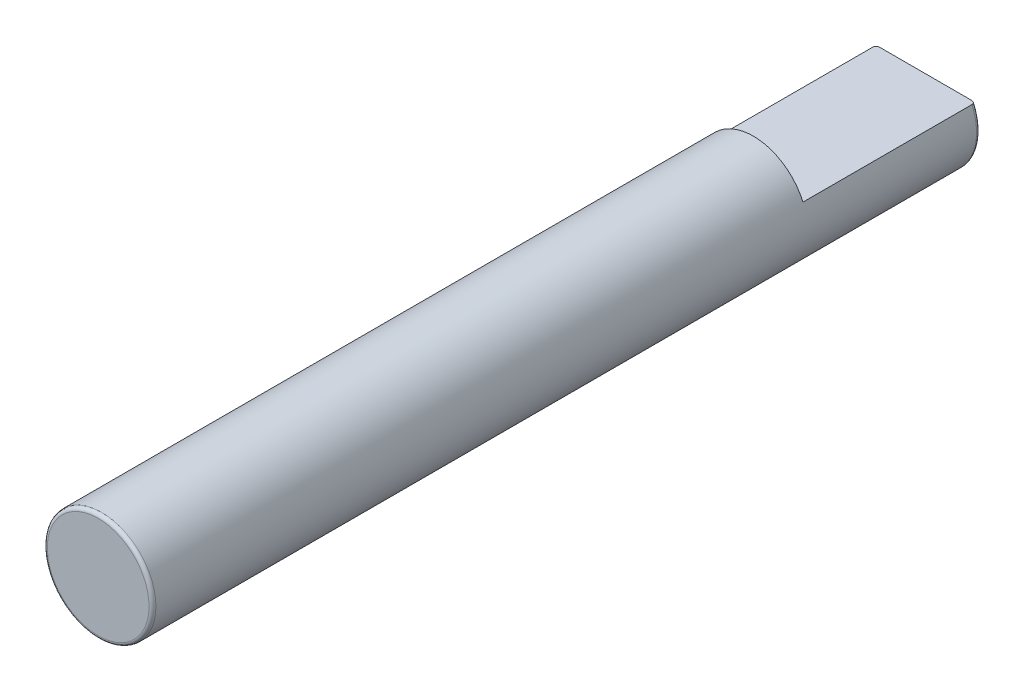
SolidWorks part; units mm, degrees
material "AISI Type 316L stainless steel"
ref_plane "Front Plane" through (0, 0, 0) normal (0, 0, 1) x (1, 0, 0)
ref_plane "Top Plane" through (0, 0, 0) normal (0, 1, 0) x (1, 0, 0)
ref_plane "Right Plane" through (0, 0, 0) normal (1, 0, 0) x (0, 0, -1)
sketch "Sketch1" plane through (0, 0, 0) normal (0, 0, 1) x (1, 0, 0)
  circle A0 centre (0, 0) radius 4
  dimension "D1" = 8
extrude "Boss-Extrude1" add sketch "Sketch1" along normal blind 60.96
fillet "Fillet2" radius 0.254 2 edges at (4, 0, 0) (4, 0, 60.96)
ref_plane "Plane1" through (0, 4, 0) normal (0, 1, 0) x (1, 0, 0)
sketch "Sketch2" plane through (0, 4, 0) normal (0, 1, 0) x (1, 0, 0)
  line L0 (4, -60.706) -> (4, -0.254) construction
  line L1 (-4, 0) -> (4, 0)
  line L2 (-4, 0) -> (-4, -12.7)
  line L3 (-4, -12.7) -> (4, -12.7)
  line L4 (4, 0) -> (4, -12.7)
  dimension "D1" = 12.7
  dimension "D2" = 8
extrude "Cut-Extrude1" cut sketch "Sketch2" against normal blind 2.3813
